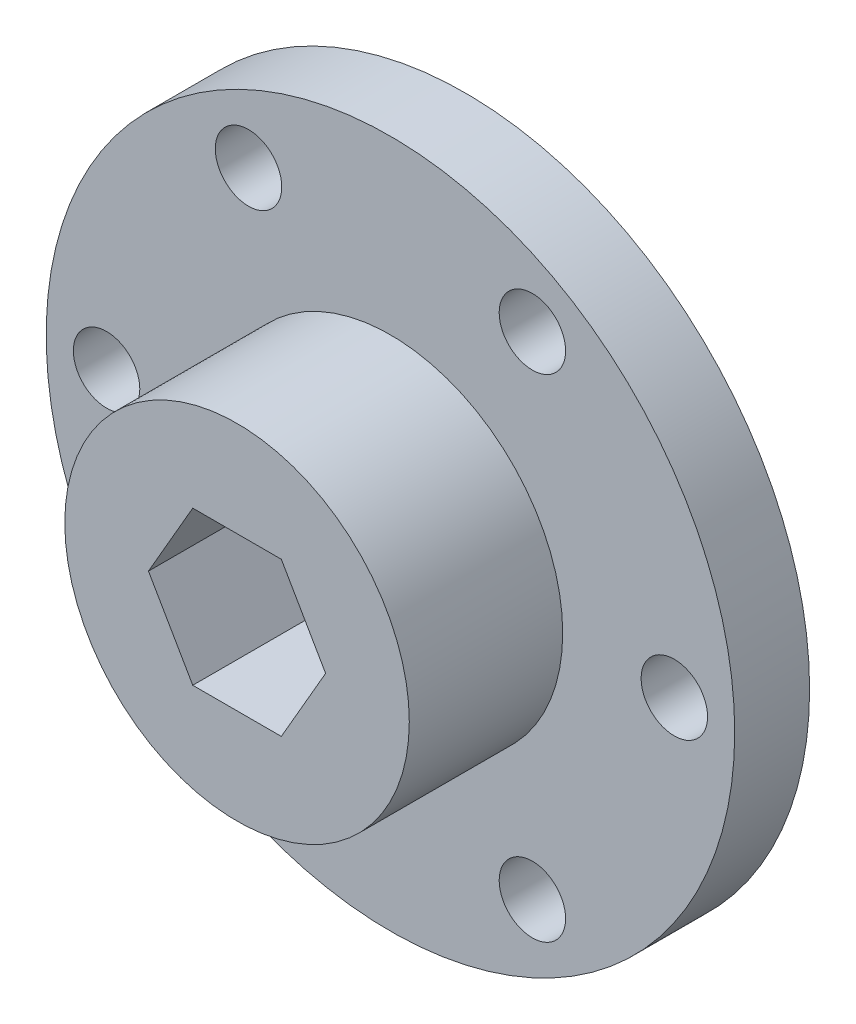
SolidWorks part; units mm, degrees
ref_plane "Front Plane" through (0, 0, 0) normal (0, 0, 1) x (1, 0, 0)
ref_plane "Top Plane" through (0, 0, 0) normal (0, 1, 0) x (1, 0, 0)
ref_plane "Right Plane" through (0, 0, 0) normal (1, 0, 0) x (0, 0, -1)
sketch "Sketch1" plane through (0, 0, 0) normal (0, 0, 1) x (1, 0, 0)
  line L1 (7.3323, 0) -> (3.6662, 6.35)
  line L2 (3.6662, 6.35) -> (-3.6662, 6.35)
  line L3 (-3.6662, 6.35) -> (-7.3323, 0)
  line L4 (-7.3323, 0) -> (-3.6662, -6.35)
  line L5 (-3.6662, -6.35) -> (3.6662, -6.35)
  line L6 (3.6662, -6.35) -> (7.3323, 0)
  circle A0 centre (0, 0) radius 28.5
  circle A1 centre (0, 0) radius 6.35 construction
  dimension "D1" = 57
  dimension "D2" = 12.7
extrude "Boss-Extrude1" add sketch "Sketch1" along normal blind 6.2
sketch "Sketch2" plane through (0, 0, 6.2) normal (0, 0, 1) x (1, 0, 0)
  line L0 (3.6662, -6.35) -> (7.3323, 0) construction
  line L1 (-3.6662, -6.35) -> (3.6662, -6.35) construction
  line L2 (-7.3323, 0) -> (-3.6662, -6.35) construction
  line L3 (-3.6662, 6.35) -> (-7.3323, 0) construction
  line L4 (7.3323, 0) -> (3.6662, 6.35) construction
  line L5 (3.6662, -6.35) -> (7.3323, 0)
  line L6 (-3.6662, -6.35) -> (3.6662, -6.35)
  line L7 (-7.3323, 0) -> (-3.6662, -6.35)
  line L8 (-3.6662, 6.35) -> (-7.3323, 0)
  line L9 (7.3323, 0) -> (3.6662, 6.35)
  line L10 (3.6662, 6.35) -> (-3.6662, 6.35) construction
  line L11 (3.6662, 6.35) -> (-3.6662, 6.35)
  circle A0 centre (0, 0) radius 14.26
  dimension "D1" = 28.52
extrude "Boss-Extrude2" add sketch "Sketch2" along normal blind 12.7
sketch "Sketch3" plane through (0, 0, 0) normal (0, 0, -1) x (-1, 0, 0)
  line L0 (-3.6662, 6.35) -> (3.6662, 6.35) construction
  line L1 (23.5, 0) -> (11.75, 20.3516) construction
  line L2 (11.75, 20.3516) -> (-11.75, 20.3516) construction
  line L3 (-11.75, 20.3516) -> (-23.5, 0) construction
  line L4 (-23.5, 0) -> (-11.75, -20.3516) construction
  line L5 (-11.75, -20.3516) -> (11.75, -20.3516) construction
  line L6 (11.75, -20.3516) -> (23.5, 0) construction
  circle A1 centre (0, 0) radius 20.3516 construction
  circle A2 centre (-11.75, 20.3516) radius 2.75
  circle A3 centre (11.75, 20.3516) radius 2.75
  circle A4 centre (23.5, 0) radius 2.75
  circle A5 centre (11.75, -20.3516) radius 2.75
  circle A6 centre (-11.75, -20.3516) radius 2.75
  circle A7 centre (-23.5, 0) radius 2.75
  dimension "D2" = 5.5
  dimension "D3" = 5.5
  dimension "D4" = 5.5
  dimension "D5" = 5.5
  dimension "D6" = 5.5
  dimension "D7" = 5.5
  dimension "D1" = 23.5
extrude "Cut-Extrude1" cut sketch "Sketch3" against normal through all
